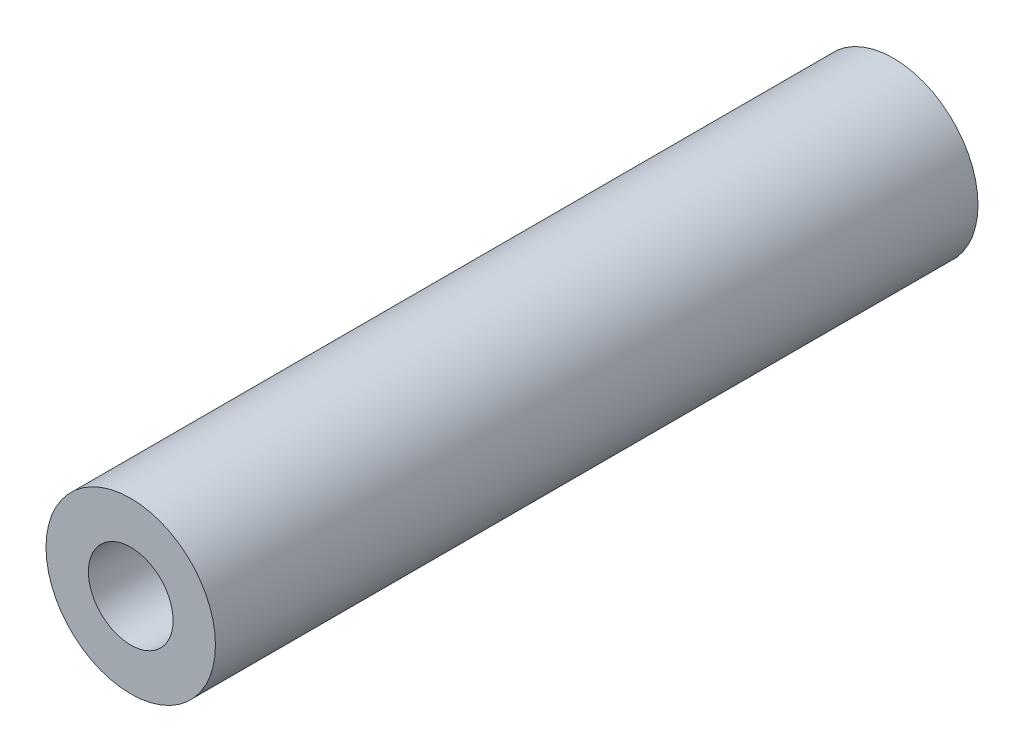
SolidWorks part; units mm, degrees
ref_plane "正面" through (0, 0, 0) normal (0, 0, 1) x (1, 0, 0)
ref_plane "平面" through (0, 0, 0) normal (0, 1, 0) x (1, 0, 0)
ref_plane "右側面" through (0, 0, 0) normal (1, 0, 0) x (0, 0, -1)
sketch "ｽｹｯﾁ1" plane through (0, 0, 0) normal (0, 0, 1) x (1, 0, 0)
  circle A0 centre (0, 0) radius 4
  circle A1 centre (0, 0) radius 2
  dimension "D1" = 8
  dimension "D2" = 4
extrude "ﾎﾞｽ - 押し出し1" add sketch "ｽｹｯﾁ1" along normal blind 36
